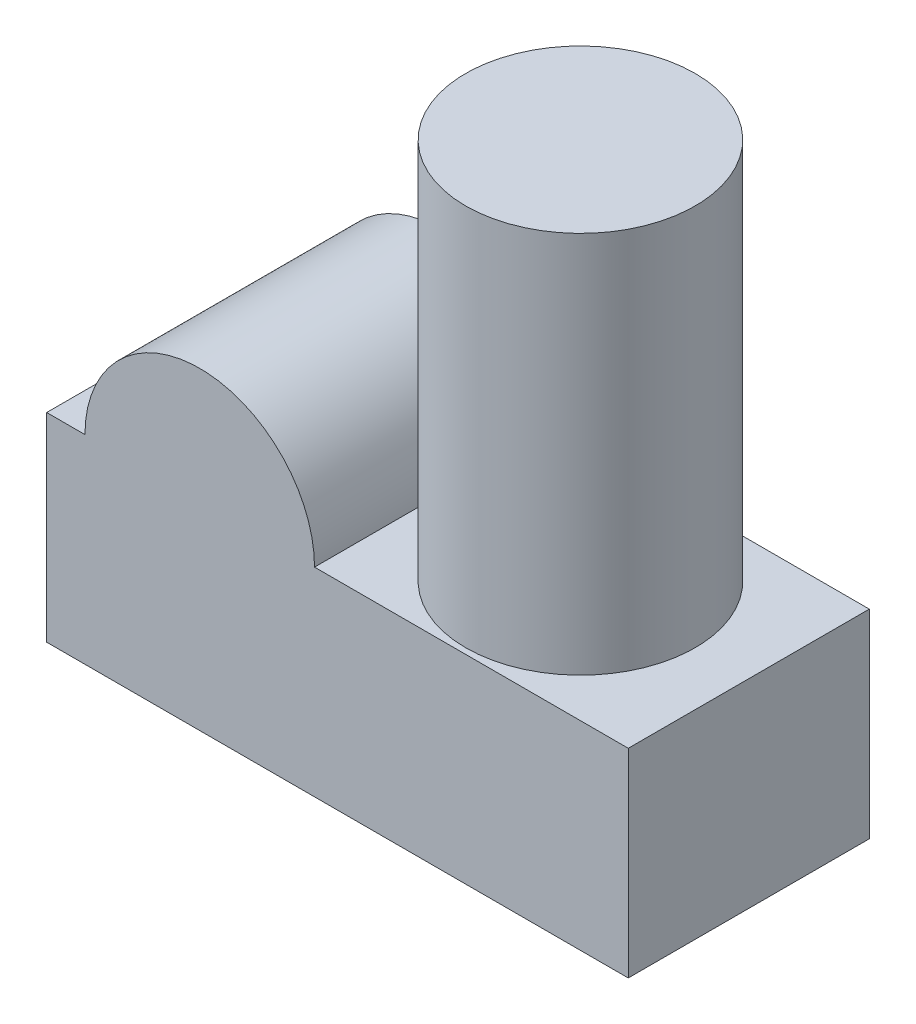
SolidWorks part; units mm, degrees
ref_plane "Plan de face" through (0, 0, 0) normal (0, 0, 1) x (1, 0, 0)
ref_plane "Plan de dessus" through (0, 0, 0) normal (0, 1, 0) x (1, 0, 0)
ref_plane "Plan de droite" through (0, 0, 0) normal (1, 0, 0) x (0, 0, -1)
sketch "Esquisse1" plane through (0, 0, 0) normal (0, 0, 1) x (1, 0, 0)
  line L0 (35, 26) -> (76, 26)
  line L1 (0, 0) -> (76, 0)
  line L2 (0, 0) -> (0, 26)
  line L3 (0, 26) -> (5, 26)
  line L4 (76, 0) -> (76, 26)
  arc A0 (35, 26) -> (5, 26) centre (20, 26) ccw
  dimension "D3" = 15
  dimension "D1" = 76
  dimension "D2" = 26
  dimension "D4" = 20
extrude "Boss.-Extru.1" add sketch "Esquisse1" along normal blind 31.5
sketch "Esquisse2" plane through (0, 26, 0) normal (0, 1, 0) x (1, 0, 0)
  line L0 (76, -31.5) -> (76, 0) construction
  circle A0 centre (54, -15.75) radius 15
  point P4 (76, -15.75)
  dimension "D1" = 30
  dimension "D2" = 22
extrude "Boss.-Extru.2" add sketch "Esquisse2" along normal blind 50
